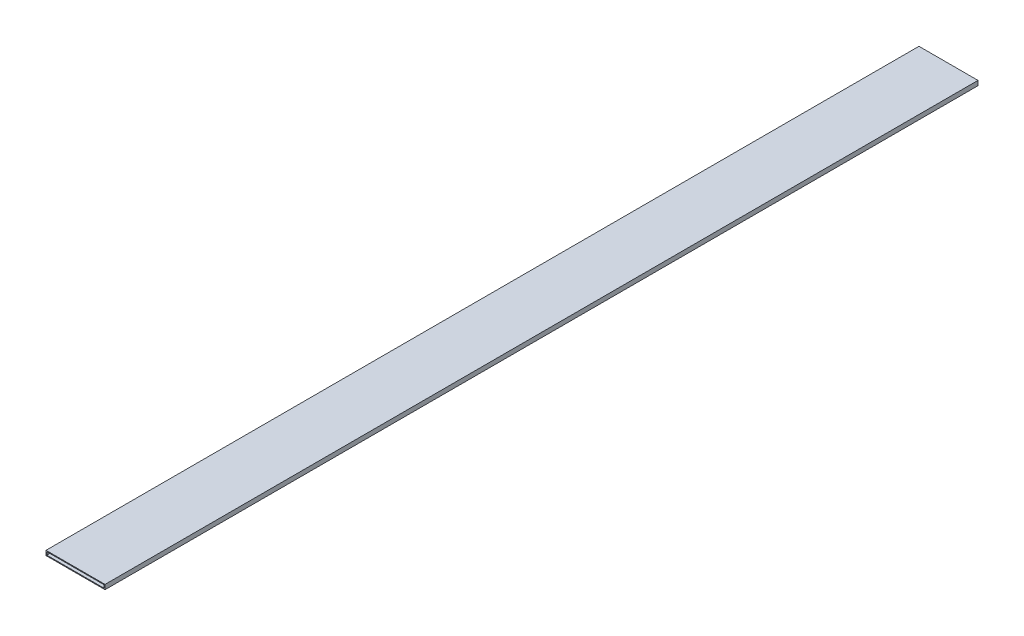
SolidWorks part; units mm, degrees
ref_plane "Front Plane" through (0, 0, 0) normal (0, 0, 1) x (1, 0, 0)
ref_plane "Top Plane" through (0, 0, 0) normal (0, 1, 0) x (1, 0, 0)
ref_plane "Right Plane" through (0, 0, 0) normal (1, 0, 0) x (0, 0, -1)
sketch "Sketch1" plane through (0, 0, 0) normal (0, 0, 1) x (1, 0, 0)
  line L1 (-1.6364, 0.5859) -> (21.3636, 0.5859)
  line L2 (-1.6364, 0.5859) -> (-1.6364, -1.2141)
  line L3 (-1.6364, -1.2141) -> (21.3636, -1.2141)
  line L4 (21.3636, 0.5859) -> (21.3636, -1.2141)
  line L5 (-1.3164, 0.2659) -> (21.0436, 0.2659)
  line L6 (-1.3164, 0.2659) -> (-1.3164, -0.8941)
  line L7 (-1.3164, -0.8941) -> (21.0436, -0.8941)
  line L8 (21.0436, 0.2659) -> (21.0436, -0.8941)
  dimension "D1" = 1.8
  dimension "D2" = 23
  dimension "D3" = 0.32
  dimension "D4" = 0.32
  dimension "D5" = 0.32
  dimension "D6" = 0.32
extrude "Boss-Extrude1" add sketch "Sketch1" along normal blind 340
